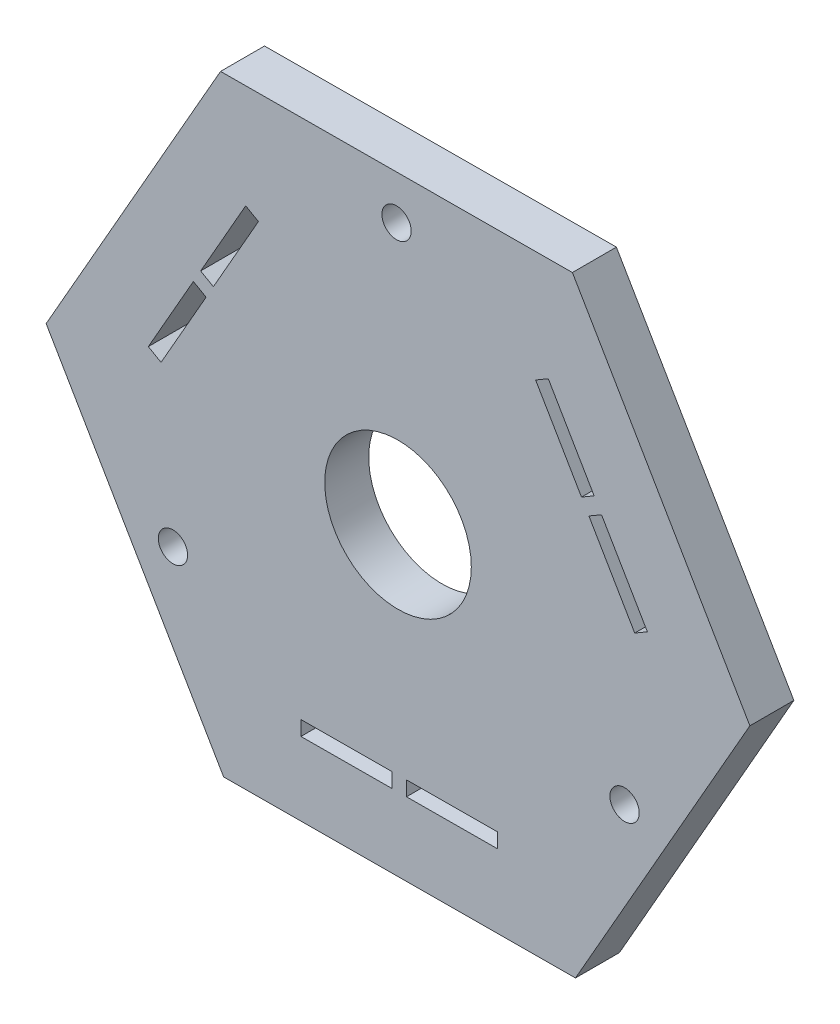
SolidWorks part; units mm, degrees
ref_plane "前视基准面" through (0, 0, 0) normal (0, 0, 1) x (1, 0, 0)
ref_plane "上视基准面" through (0, 0, 0) normal (0, 1, 0) x (1, 0, 0)
ref_plane "右视基准面" through (0, 0, 0) normal (1, 0, 0) x (0, 0, -1)
other "Configuration Table"
sketch "草图1" plane through (0, 0, 0) normal (0, 0, 1) x (1, 0, 0)
  line L1 (11.8953, 20.8451) -> (-12.1047, 20.7242)
  line L2 (-12.1047, 20.7242) -> (-24, -0.1209)
  line L3 (-24, -0.1209) -> (-11.8953, -20.8451)
  line L4 (-11.8953, -20.8451) -> (12.1047, -20.7242)
  line L5 (12.1047, -20.7242) -> (24, 0.1209)
  line L6 (24, 0.1209) -> (11.8953, 20.8451)
  circle A0 centre (0, 0) radius 20.7849 construction
  dimension "D1" = 24
extrude "凸台-拉伸1" add sketch "草图1" along normal blind 3
sketch "草图2" plane through (0, 0, 3) normal (0, 0, 1) x (1, 0, 0)
  line L0 (10.251, 13.7466) -> (9.3875, 13.2423)
  line L1 (9.3875, 13.2423) -> (12.5145, 7.8886)
  line L2 (12.5145, 7.8886) -> (13.378, 8.393)
  line L3 (13.378, 8.393) -> (10.251, 13.7466)
  line L4 (24, 0.1209) -> (11.8953, 20.8451) construction
  line L5 (17.9476, 10.483) -> (10.1982, 5.9566) construction
  line L6 (13.0188, 7.0251) -> (13.8823, 7.5295)
  line L7 (16.1459, 1.6714) -> (13.0188, 7.0251)
  line L8 (13.8823, 7.5295) -> (17.0094, 2.1758)
  line L9 (17.0094, 2.1758) -> (16.1459, 1.6714)
  line L10 (6.7794, -15.7509) -> (6.7744, -14.7509)
  line L11 (6.7744, -14.7509) -> (0.5745, -14.7822)
  line L12 (0.5795, -15.7822) -> (6.7794, -15.7509)
  line L13 (0.5745, -14.7822) -> (0.5795, -15.7822)
  line L14 (-0.4255, -14.7872) -> (-0.4205, -15.7872)
  line L15 (-6.6254, -14.8184) -> (-0.4255, -14.7872)
  line L16 (-0.4205, -15.7872) -> (-6.6204, -15.8184)
  line L17 (-6.6204, -15.8184) -> (-6.6254, -14.8184)
  line L18 (-17.0304, 2.0043) -> (-16.1619, 1.5087)
  line L19 (-16.1619, 1.5087) -> (-13.089, 6.8936)
  line L20 (-13.9575, 7.3892) -> (-17.0304, 2.0043)
  line L21 (-13.089, 6.8936) -> (-13.9575, 7.3892)
  line L22 (-12.5933, 7.7621) -> (-13.4619, 8.2577)
  line L23 (-9.5204, 13.147) -> (-12.5933, 7.7621)
  line L24 (-13.4619, 8.2577) -> (-10.389, 13.6426)
  line L25 (-10.389, 13.6426) -> (-9.5204, 13.147)
  point P32 (0, 0)
  dimension "D1" = 5
  dimension "D2" = 1
  dimension "D3" = 0.5
  dimension "D4" = 6.2
  dimension "D5" = 3
extrude "切除-拉伸1" cut sketch "草图2" against normal blind 3
sketch "草图3" plane through (0, 0, 3) normal (0, 0, 1) x (1, 0, 0)
  circle A0 centre (0, 0) radius 5
  dimension "D1" = 10
extrude "切除-拉伸2" cut sketch "草图3" against normal blind 3
sketch "草图6" plane through (0, 0, 3) normal (0, 0, 1) x (1, 0, 0)
  line L0 (11.8953, 20.8451) -> (-12.1047, 20.7242) construction
  circle A0 centre (-0.1005, 17.7846) radius 1
  circle A1 centre (15.4521, -8.8053) radius 1
  circle A2 centre (-15.3517, -8.9793) radius 1
  point P11 (0, 0)
  dimension "D1" = 2
  dimension "D2" = 3
  dimension "D3" = 3
extrude "切除-拉伸3" cut sketch "草图6" against normal blind 3
